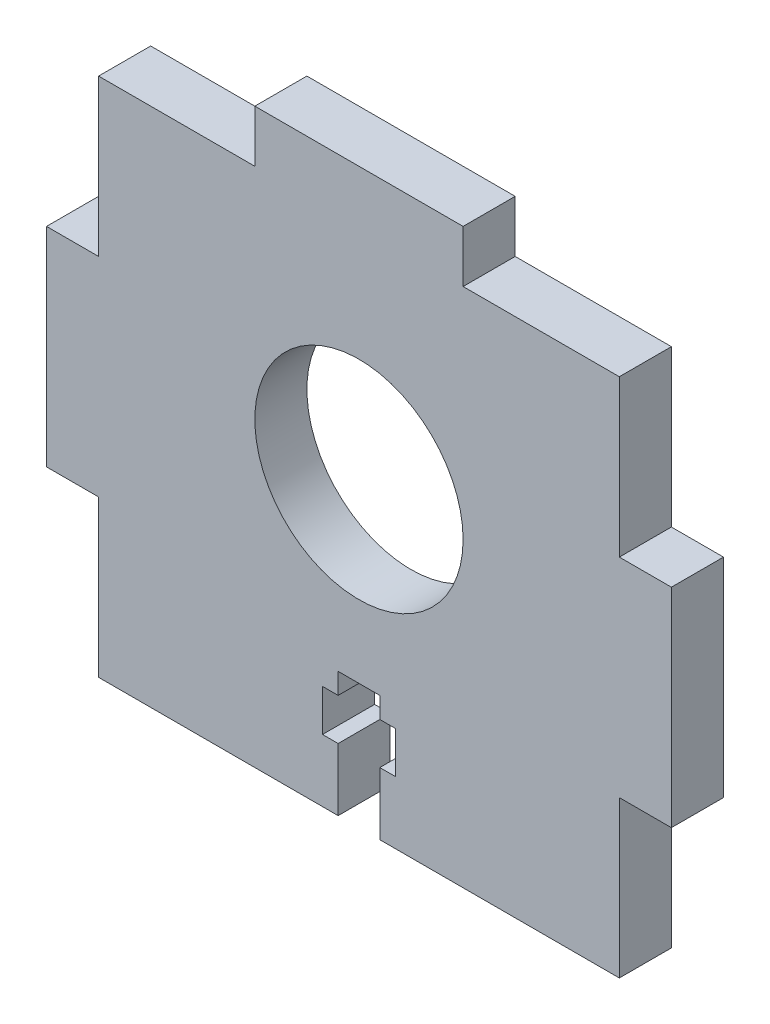
SolidWorks part; units mm, degrees
ref_plane "Front Plane" through (0, 0, 0) normal (0, 0, 1) x (1, 0, 0)
ref_plane "Top Plane" through (0, 0, 0) normal (0, 1, 0) x (1, 0, 0)
ref_plane "Right Plane" through (0, 0, 0) normal (1, 0, 0) x (0, 0, -1)
sketch "Sketch2" plane through (0, 0, 0) normal (0, 0, 1) x (1, 0, 0)
  line L0 (-28.8736, 4.87) -> (31.7513, 4.87) construction
  line L1 (-26.7513, 29.87) -> (-11.7513, 29.87)
  line L2 (-26.7513, 29.87) -> (-26.7513, 14.87)
  line L3 (-26.7513, -20.13) -> (23.2487, -20.13)
  line L4 (23.2487, 29.87) -> (23.2487, 14.87)
  line L5 (-26.7513, 29.87) -> (23.2487, -20.13) construction
  line L6 (-26.7513, -20.13) -> (23.2487, 29.87) construction
  line L7 (-1.7513, 39.7912) -> (-1.7513, -39.7912) construction
  line L8 (-11.7513, 29.87) -> (-11.7513, 34.87)
  line L9 (23.2487, 14.87) -> (28.2487, 14.87)
  line L10 (28.2487, 14.87) -> (28.2487, -5.13)
  line L11 (23.2487, -5.13) -> (28.2487, -5.13)
  line L12 (-11.7513, 34.87) -> (8.2487, 34.87)
  line L13 (8.2487, 29.87) -> (8.2487, 34.87)
  line L14 (-26.7513, -5.13) -> (-31.7513, -5.13)
  line L15 (-31.7513, -5.13) -> (-31.7513, 14.87)
  line L16 (-26.7513, 14.87) -> (-31.7513, 14.87)
  line L17 (8.2487, 29.87) -> (23.2487, 29.87)
  line L18 (-26.7513, -5.13) -> (-26.7513, -20.13)
  line L19 (23.2487, -5.13) -> (23.2487, -20.13)
  point P0 (-1.7513, 4.87)
  point P21 (-1.7513, 4.87)
  dimension "D1" = 50
  dimension "D2" = 5
  dimension "D3" = 5
extrude "Boss-Extrude1" add sketch "Sketch2" along normal blind 5
sketch "Sketch3" plane through (0, 0, 5) normal (0, 0, 1) x (1, 0, 0)
  line L0 (-3.7513, -20.13) -> (-3.7513, -14.13)
  line L1 (-3.7513, -14.13) -> (-5.2513, -14.13)
  line L2 (-5.2513, -14.13) -> (-5.2513, -10.13)
  line L3 (-5.2513, -10.13) -> (-3.7513, -10.13)
  line L4 (-3.7513, -10.13) -> (-3.7513, -8.13)
  line L5 (-3.7513, -8.13) -> (0.2487, -8.13)
  line L6 (0.2487, -8.13) -> (0.2487, -10.13)
  line L7 (0.2487, -10.13) -> (1.7487, -10.13)
  line L8 (1.7487, -10.13) -> (1.7487, -14.13)
  line L9 (1.7487, -14.13) -> (0.2487, -14.13)
  line L10 (0.2487, -14.13) -> (0.2487, -20.13)
  line L11 (0.2487, -20.13) -> (-3.7513, -20.13)
  line L13 (-1.7513, -20.13) -> (-1.7513, 0) construction
  line L14 (-26.7513, -20.13) -> (23.2487, -20.13) construction
  circle A0 centre (-1.7513, 8.828) radius 10
  dimension "D1" = 20
  dimension "D2" = 9
  dimension "D3" = 12
  dimension "D4" = 6
  dimension "D5" = 4
  dimension "D6" = 1.5
  dimension "D7" = 4
  dimension "D8" = 0
  dimension "D9" = 2
extrude "Cut-Extrude1" cut sketch "Sketch3" against normal blind 5
